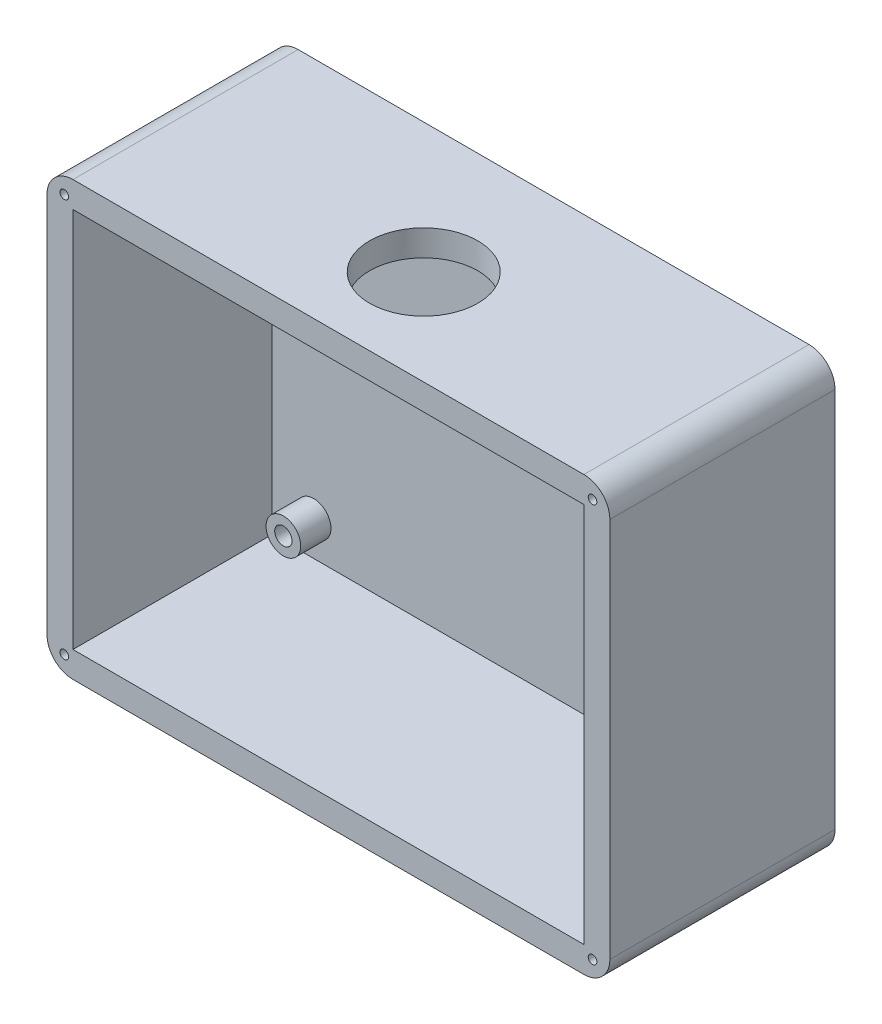
SolidWorks part; units mm, degrees
ref_plane "Ebene vorne" through (0, 0, 0) normal (0, 0, 1) x (1, 0, 0)
ref_plane "Ebene oben" through (0, 0, 0) normal (0, 1, 0) x (1, 0, 0)
ref_plane "Ebene rechts" through (0, 0, 0) normal (1, 0, 0) x (0, 0, -1)
sketch "Skizze1" plane through (0, 0, 0) normal (0, 0, 1) x (1, 0, 0)
  line L1 (0, 0) -> (65, 0)
  line L2 (0, 0) -> (0, -50)
  line L3 (0, -50) -> (65, -50)
  line L4 (65, 0) -> (65, -50)
  dimension "D1" = 50
  dimension "D2" = 65
extrude "Aufsatz-Linear austragen1" add sketch "Skizze1" along normal blind 3
sketch "Skizze2" plane through (0, 0, 3) normal (0, 0, 1) x (1, 0, 0)
  line L0 (3, -3) -> (3, -47)
  line L1 (0, 0) -> (65, 0)
  line L2 (0, 0) -> (0, -50)
  line L3 (0, -50) -> (65, -50)
  line L4 (65, 0) -> (65, -50)
  line L5 (3, -47) -> (62, -47)
  line L6 (62, -3) -> (62, -47)
  line L7 (3, -3) -> (62, -3)
  dimension "D1" = 3
extrude "Aufsatz-Linear austragen2" add sketch "Skizze2" along normal blind 23
sketch "Skizze4" plane through (0, 0, 3) normal (0, 0, 1) x (1, 0, 0)
  line L0 (3, -47) -> (62, -47) construction
  circle A0 centre (7.7978, -7) radius 2
  circle A1 centre (56.7978, -7) radius 2
  circle A2 centre (56.7978, -43) radius 2
  circle A3 centre (7.7978, -43) radius 2
  circle A4 centre (7.7978, -7) radius 1
  circle A5 centre (56.7978, -7) radius 1
  circle A6 centre (56.7978, -43) radius 1
  circle A7 centre (7.7978, -43) radius 1
  dimension "D1" = 49
  dimension "D2" = 36
  dimension "D3" = 4
  dimension "D4" = 36
  dimension "D5" = 49
  dimension "D6" = 1
extrude "Aufsatz-Linear austragen3" add sketch "Skizze4" along normal blind 3.5
sketch "Skizze5" plane through (0, 0, 0) normal (0, 1, 0) x (1, 0, 0)
  line L0 (65, 0) -> (0, 0) construction
  line L1 (65, -26) -> (0, -26) construction
  circle A0 centre (32.5, -15) radius 6.25
  point P4 (32.5, -26)
  dimension "D1" = 15
  dimension "D2" = 0
extrude "Schnitt-Linear austragen1" cut sketch "Skizze5" against normal up to next
fillet "Verrundung1" radius 3 4 edges at (0, 0, 13) (65, 0, 13) (65, -50, 13) (0, -50, 13)
hole_wizard "Ø1.0 (1) Durchmesser Bohrung1" positions "Skizze7" profile "Skizze6" hole size "Ø1.0" standard "ANSI Metrisch"
sketch "Skizze7" plane through (0, 0, 26) normal (0, 0, 1) x (1, 0, 0)
  line L0 (3, -50) -> (62, -50) construction
  line L1 (65, -47) -> (65, -3) construction
  line L2 (62, 0) -> (3, 0) construction
  line L3 (0, -3) -> (0, -47) construction
  point P0 (63, -48)
  point P2 (63, -2)
  point P4 (2, -2)
  point P6 (2, -48)
  dimension "D1" = 2
  dimension "D2" = 2
  dimension "D3" = 2
  dimension "D4" = 2
  dimension "D5" = 2
  dimension "D6" = 2
  dimension "D7" = 2
  dimension "D8" = 2
sketch "Skizze6" plane through (63, -48, 26) normal (1, 0, 0) x (0, -1, 0)
  line L0 (0, 0) -> (0, 15.3004)
  line L1 (0, 15.3004) -> (0.5, 15)
  line L2 (0.5, 15) -> (0.5, 0)
  line L5 (0.5, 0) -> (0, 0)
  line L10 (0, 15.3004) -> (-0.5, 15) construction
  line L11 (0, -6.35) -> (0, 107.95) construction
  dimension "Bohrerdurchmesser" = 1
  dimension "Bohrungstiefe" = 15
  dimension "Spitzenwinkel" = 118
